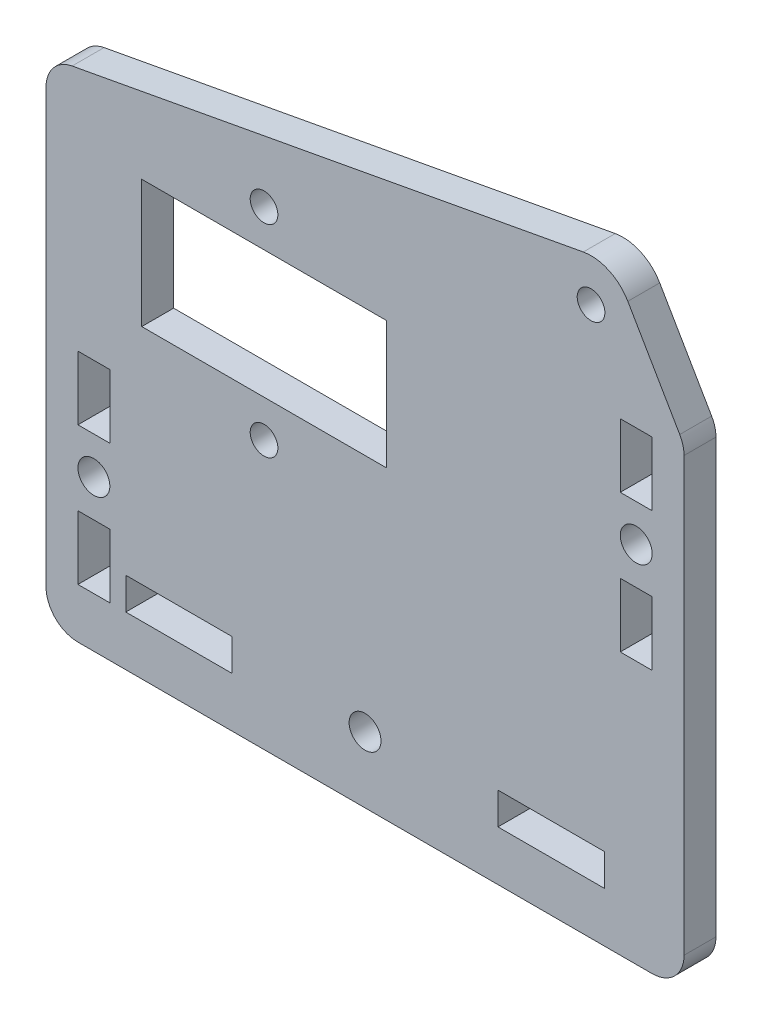
SolidWorks part; units mm, degrees
ref_plane "Front Plane" through (0, 0, 0) normal (0, 0, 1) x (1, 0, 0)
ref_plane "Top Plane" through (0, 0, 0) normal (0, 1, 0) x (1, 0, 0)
ref_plane "Right Plane" through (0, 0, 0) normal (1, 0, 0) x (0, 0, -1)
sketch "Model" plane through (0, 0, 0) normal (0, 0, 1) x (1, 0, 0)
  line L0 (24.9516, 51.8575) -> (24.9516, 11.1577)
  line L1 (27.4063, 54.8075) -> (75.4768, 63.6956)
  line L2 (79.663, 61.7713) -> (84.5459, 53.3643)
  line L3 (84.9517, 11.1574) -> (84.9518, 51.8575)
  line L4 (30.9518, 25.8575) -> (30.9518, 31.8575)
  line L5 (30.9518, 31.8575) -> (27.9518, 31.8575)
  line L6 (27.9518, 31.8575) -> (27.9518, 25.8575)
  line L7 (27.9518, 25.8575) -> (30.9518, 25.8575)
  line L8 (33.9518, 48.8575) -> (56.9518, 48.8575)
  line L9 (56.9518, 48.8575) -> (56.9518, 36.8575)
  line L10 (56.9518, 36.8575) -> (33.9518, 36.8575)
  line L11 (33.9518, 36.8575) -> (33.9518, 48.8575)
  line L12 (27.9518, 18.8575) -> (30.9518, 18.8575)
  line L13 (27.9518, 12.8575) -> (30.9518, 12.8575)
  line L14 (27.9518, 18.8575) -> (27.9518, 12.8575)
  line L15 (30.9518, 12.8575) -> (30.9518, 18.8575)
  line L16 (32.4518, 12.8575) -> (42.4518, 12.8575)
  line L17 (32.4518, 15.8575) -> (42.4518, 15.8575)
  line L18 (32.4518, 12.8575) -> (32.4518, 15.8575)
  line L19 (42.4518, 15.8575) -> (42.4518, 12.8575)
  line L20 (67.4518, 12.8575) -> (67.4518, 15.8575)
  line L21 (77.4518, 15.8575) -> (77.4518, 12.8575)
  line L22 (67.4518, 15.8575) -> (77.4518, 15.8575)
  line L23 (77.4518, 12.8575) -> (67.4518, 12.8575)
  line L24 (78.9518, 38.8575) -> (81.9518, 38.8575)
  line L25 (78.9518, 32.8575) -> (81.9518, 32.8575)
  line L26 (78.9518, 32.8575) -> (78.9518, 38.8575)
  line L27 (81.9518, 32.8575) -> (81.9518, 38.8575)
  line L28 (78.9518, 51.8575) -> (81.9518, 51.8575)
  line L29 (78.9518, 45.8575) -> (81.9518, 45.8575)
  line L30 (81.9518, 45.8575) -> (81.9518, 51.8575)
  line L31 (78.9518, 45.8575) -> (78.9518, 51.8575)
  line L32 (27.9518, 8.1575) -> (81.9518, 8.1575)
  arc A0 (84.9518, 51.8575) -> (84.5459, 53.3643) centre (81.9514, 51.8573) ccw
  arc A1 (79.663, 61.7713) -> (75.4768, 63.6956) centre (76.2041, 59.7622) ccw
  arc A2 (27.4063, 54.8075) -> (24.9516, 51.8575) centre (27.9517, 51.8574) ccw
  arc A3 (24.9516, 11.1577) -> (27.9518, 8.1575) centre (27.9519, 11.1577) ccw
  arc A4 (81.9518, 8.1575) -> (84.9517, 11.1574) centre (81.9517, 11.1574) ccw
  circle A5 centre (45.4516, 52.3575) radius 1.3
  circle A6 centre (45.4518, 33.3575) radius 1.3
  circle A7 centre (76.2041, 59.7623) radius 1.3
  circle A8 centre (54.9517, 14.3575) radius 1.5
  circle A9 centre (29.4518, 22.3575) radius 1.5
  circle A10 centre (80.4518, 42.3575) radius 1.5
extrude "Boss-Extrude1" add sketch "Model" along normal blind 3
